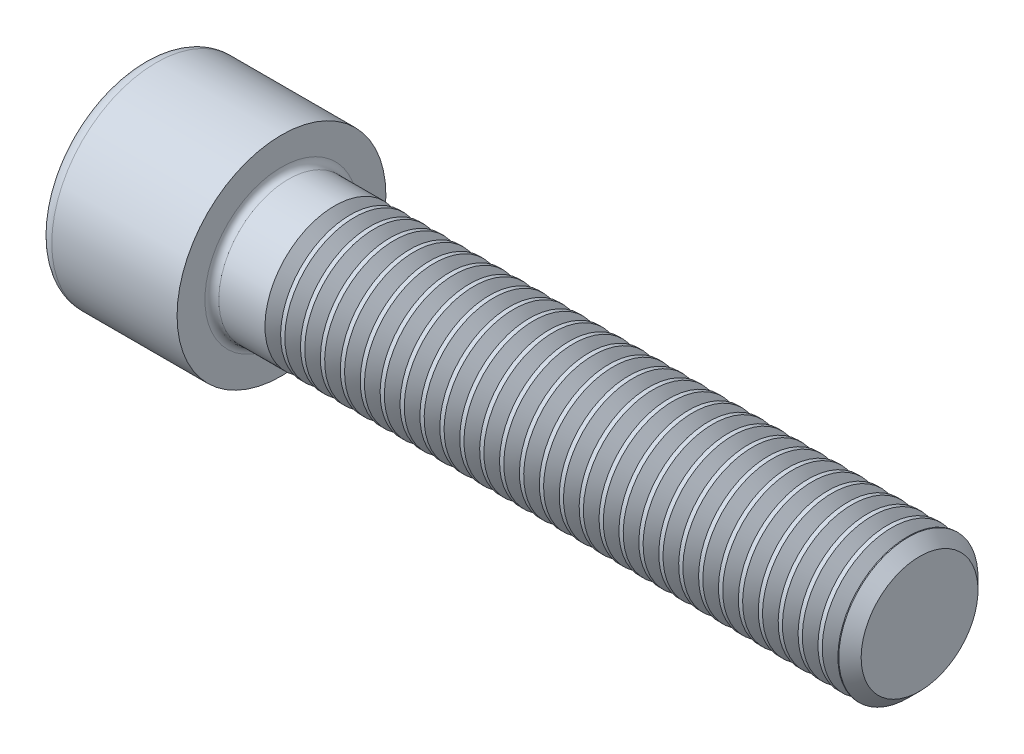
SolidWorks part; units mm, degrees
revolve "Base-Revolve" add sketch "BodySke"
sketch "BodySke" plane through (0, 0, 0) normal (0, 0, 1) x (1, 0, 0)
  line L0 (0, 0) -> (0, 9)
  line L1 (0, 9) -> (12, 9)
  line L2 (12, 9) -> (12, 6)
  line L3 (12, 6) -> (66.036, 6)
  line L4 (67, 5.036) -> (67, 0)
  line L5 (67, 0) -> (0, 0)
  line L6 (-31.75, 0) -> (127, 0) construction
  line L8 (67, 5.036) -> (66.036, 6)
  line L10 (67, -5.036) -> (66.036, -6) construction
  line L11 (13.75, 9.525) -> (13.75, 3.175) construction
  line L12 (12, 9.525) -> (12, 3.175) construction
  line L13 (7, 9.525) -> (7, 3.175) construction
cosmetic thread "ThreadCosmetic" [suppressed]
fillet "Fillet1" radius 0.6 1 edges at (12, 0, 6)
fillet "Fillet2" radius 1.2 1 edges at (0, 0, 9)
ref_plane "Plane1" through (0, 0, 0) normal (0, 0, 1) x (1, 0, 0)
ref_plane "Plane2" through (0, 0, 0) normal (0, 1, 0) x (1, 0, 0)
ref_plane "Plane3" through (0, 0, 0) normal (1, 0, 0) x (0, 0, -1)
sketch "Sketch2" plane through (0, 0, 0) normal (0, 0, 1) x (1, 0, 0)
  line L0 (0, 5.0125) -> (6, 5.0125)
  line L1 (6, 5.0125) -> (8.894, 0)
  line L2 (-31.75, 0) -> (127, 0) construction
  line L3 (8.894, 0) -> (0, 0)
  line L4 (0, 0) -> (0, 5.0125)
  line L6 (0, 0) -> (47.625, 0) construction
revolve "Hex-PreBroach" cut sketch "Sketch2" angle 360 about L6
sketch "Sketch3" plane through (0, 0, 0) normal (-1, 0, 0) x (0, 0.5, 0.866)
  line L0 (2.894, 5.0125) -> (-2.894, 5.0125)
  line L1 (-2.894, 5.0125) -> (-5.7879, 0)
  line L2 (2.894, 5.0125) -> (5.7879, 0)
  line L3 (2.894, -5.0125) -> (5.7879, 0)
  line L4 (2.894, -5.0125) -> (-2.894, -5.0125)
  line L5 (-2.894, -5.0125) -> (-5.7879, 0)
extrude "Hex" cut sketch "Sketch3" against normal blind 6
sketch "ThdSchSke" plane through (0, 0, 0) normal (0, 0, 1) x (1, 0, 0)
  line L0 (17.25, -5.036) -> (16.575, -6)
  line L1 (17.25, -5.036) -> (17.925, -6)
  line L2 (17.925, -6) -> (17.925, -7.5)
  line L3 (-3.175, 0) -> (5.1513, 0) construction
  line L4 (0, 7.8) -> (0, -7.8) construction
  line L5 (17.925, -7.5) -> (16.575, -7.5)
  line L6 (16.575, -7.5) -> (16.575, -6)
revolve "ThreadSchematic" cut sketch "ThdSchSke" angle 360 about L3
pattern_linear "ThdSchPat" count 29 spacing 1.7155 along (1, 0, 0) of "ThreadSchematic"
equation "\"D2@Sketch3\" = \"Hex_size@Sketch3\" / 2"
equation "\"D1@Sketch3\" = \"Hex_size@Sketch3\" / 2"
equation "\"D1@Sketch2\" = \"Hex_size@Sketch3\" / 2"
equation "\"Thread_minor@ThreadCosmetic\"  =  \"Minor_dia@BodySke\""
equation "\"Depth@Sketch2\" =  \"Key_eng@Hex\""
equation "\"Thread_length@ThreadCosmetic\" = ((sgn( (\"Length@BodySke\" - \"Advance@BodySke\" * 3.0) - \"Thread_nom@BodySke\" )-1)*( (\"Length@BodySke\" - \"Advance@BodySke\" * 3.0) - \"Thread_nom@BodySke\" ))/-2+ \"Thread_nom@BodySke\""
equation "\"Thread_minor@ThdSchSke\" = \"Minor_dia@BodySke\""
equation "\"Diameter@ThdSchSke\" = \"Diameter@BodySke\""
equation "\"Overcut@ThdSchSke\" = \"Diameter@BodySke\" * 1.25"
equation "\"Start@ThdSchSke\" = \"Head_ht@BodySke\" + \"Length@BodySke\" - \"Thread_length@ThreadCosmetic\"  '---Non-countersunk---"
equation "\"Num_threads@ThdSchPat\" = int( \"Thread_length@ThreadCosmetic\" / \"Advance@BodySke\" + 0.999 )  + 1"
equation "\"Advance@ThdSchPat\" = \"Thread_length@ThreadCosmetic\" /  (\"Num_threads@ThdSchPat\" - 1) 'relax it"
equation "\"Num_threads@ThdSchPat\" = \"Num_threads@ThdSchPat\" - sgn( \"Num_threads@ThdSchPat\" - 1) '---chamfered tips only---"
